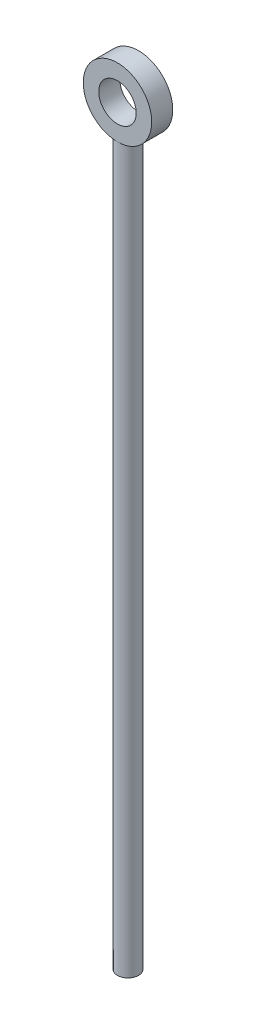
SolidWorks part; units mm, degrees
ref_plane "Front Plane" through (0, 0, 0) normal (0, 0, 1) x (1, 0, 0)
ref_plane "Top Plane" through (0, 0, 0) normal (0, 1, 0) x (1, 0, 0)
ref_plane "Right Plane" through (0, 0, 0) normal (1, 0, 0) x (0, 0, -1)
sketch "Sketch1" plane through (0, 0, 0) normal (0, 1, 0) x (1, 0, 0)
  circle A0 centre (0, 0) radius 0.5
  dimension "D1" = 1
extrude "Boss-Extrude1" add sketch "Sketch1" along normal blind 35
sketch "Sketch2" plane through (0, 0, 0) normal (0, 0, 1) x (1, 0, 0)
  circle A0 centre (0, 35.8898) radius 0.8898
  circle A1 centre (0, 35.8898) radius 1.6242
extrude "Boss-Extrude2" add sketch "Sketch2" along normal mid plane 1
